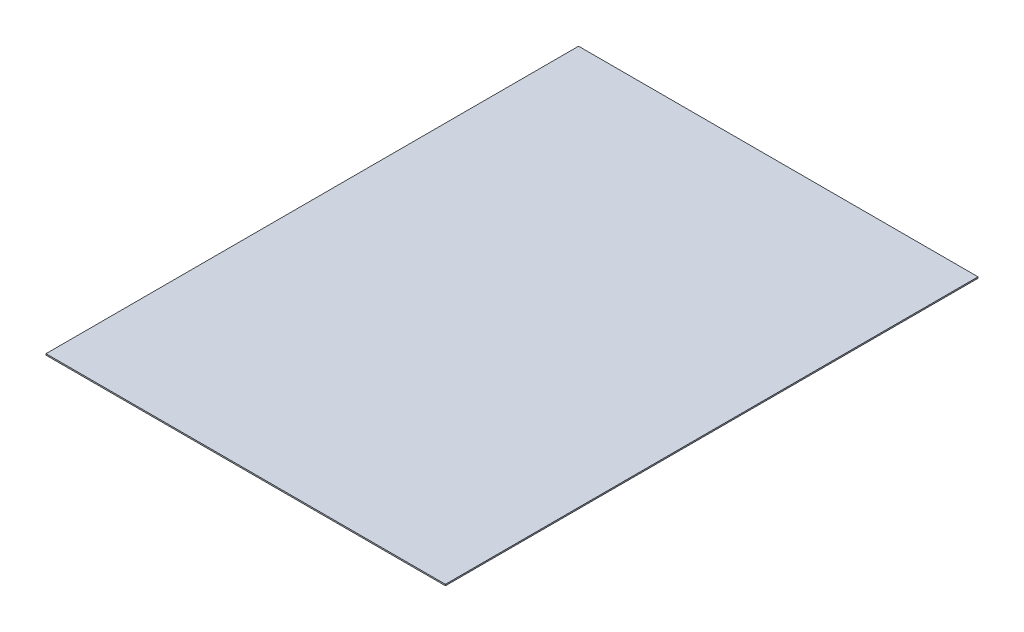
SolidWorks part; units mm, degrees
material "陶瓷"
ref_plane "前视基准面" through (0, 0, 0) normal (0, 0, 1) x (1, 0, 0)
ref_plane "上视基准面" through (0, 0, 0) normal (0, 1, 0) x (1, 0, 0)
ref_plane "右视基准面" through (0, 0, 0) normal (1, 0, 0) x (0, 0, -1)
sketch "草图1" plane through (0, 0, 0) normal (0, 1, 0) x (1, 0, 0)
  line L1 (-1500, -2000) -> (1500, -2000)
  line L2 (-1500, -2000) -> (-1500, 2000)
  line L3 (-1500, 2000) -> (1500, 2000)
  line L4 (1500, -2000) -> (1500, 2000)
  line L5 (-1500, -2000) -> (1500, 2000) construction
  line L6 (-1500, 2000) -> (1500, -2000) construction
  point P0 (0, 0)
  dimension "D1" = 3000
  dimension "D2" = 4000
extrude "凸台-拉伸1" add sketch "草图1" along normal blind 10
